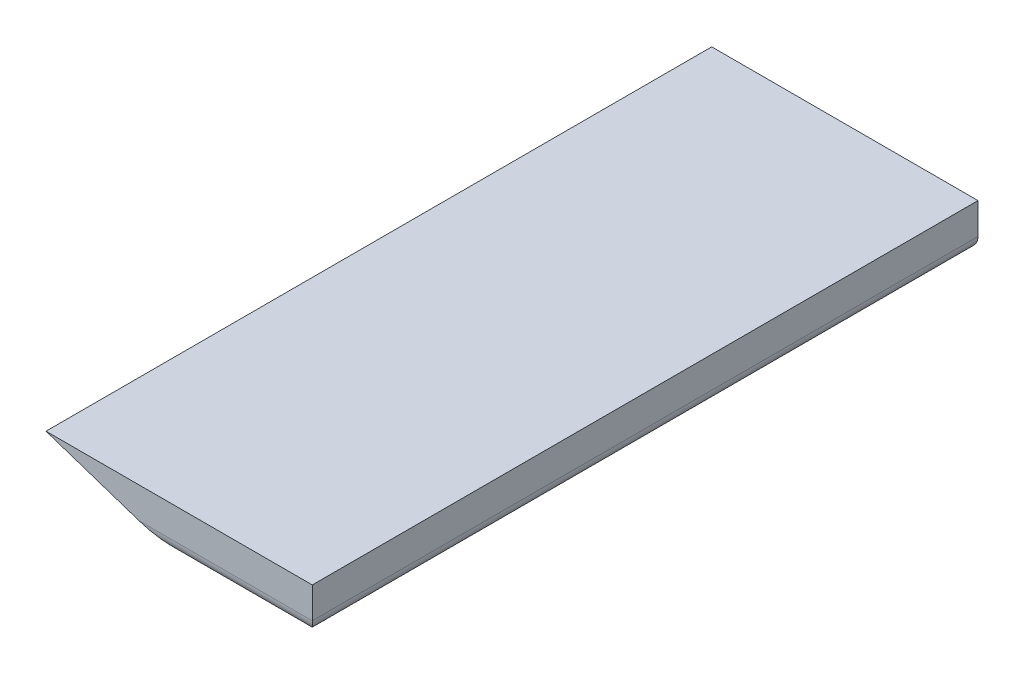
SolidWorks part; units mm, degrees
ref_plane "Front Plane" through (0, 0, 0) normal (0, 0, 1) x (1, 0, 0)
ref_plane "Top Plane" through (0, 0, 0) normal (0, 1, 0) x (1, 0, 0)
ref_plane "Right Plane" through (0, 0, 0) normal (1, 0, 0) x (0, 0, -1)
sketch "Sketch1" plane through (0, 0, 0) normal (0, 0, 1) x (1, 0, 0)
  line L1 (-30, -5) -> (30, -5)
  line L2 (-30, -5) -> (-30, 5)
  line L3 (-30, 5) -> (30, 5)
  line L4 (30, -5) -> (30, 5)
  line L5 (-30, -5) -> (30, 5) construction
  line L6 (-30, 5) -> (30, -5) construction
  point P0 (0, 0)
  dimension "D1" = 10
  dimension "D2" = 60
extrude "Boss-Extrude1" add sketch "Sketch1" along normal blind 150
sketch "Sketch2" plane through (0, 0, 150) normal (0, 0, 1) x (1, 0, 0)
  line L0 (-30, 5) -> (-30, -5)
  line L1 (-30, -5) -> (0, -5)
  line L4 (0, -5) -> (-30, 5)
extrude "Cut-Extrude1" cut sketch "Sketch2" against normal blind 50 contours L4 L0 L1
fillet "Fillet1" radius 3 4 edges at (30, -5, 75) (-30, -5, 50) (-15, -5, 100) (15, -5, 150)
